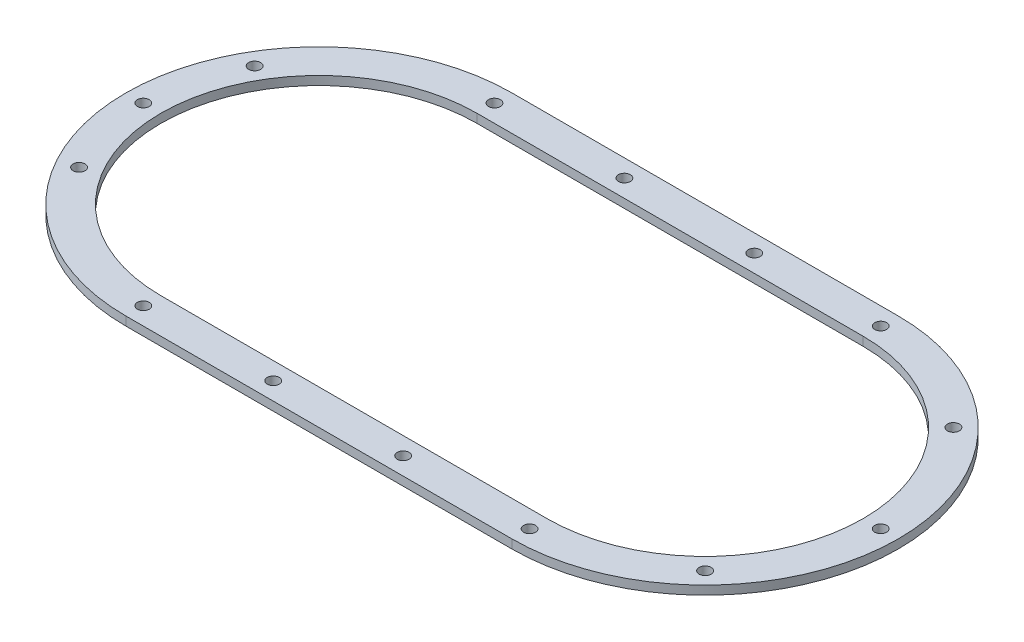
SolidWorks part; units mm, degrees
ref_plane "Front Plane" through (0, 0, 0) normal (0, 0, 1) x (1, 0, 0)
ref_plane "Top Plane" through (0, 0, 0) normal (0, 1, 0) x (1, 0, 0)
ref_plane "Right Plane" through (0, 0, 0) normal (1, 0, 0) x (0, 0, -1)
sketch "Sketch1" plane through (0, 0, 0) normal (0, 1, 0) x (1, 0, 0)
  line L0 (0, 0) -> (220, 0) construction
  line L1 (0, 110) -> (220, 110)
  line L2 (0, -110) -> (220, -110)
  line L3 (0, 90) -> (220, 90)
  line L4 (0, -90) -> (220, -90)
  line L5 (0, 100) -> (220, 100) construction
  line L6 (0, -100) -> (220, -100) construction
  line L7 (-110, 0) -> (330, 0) construction
  line L8 (0, 0) -> (-95.2628, 55) construction
  line L9 (220, 0) -> (297.7817, 77.7817) construction
  arc A0 (0, 110) -> (0, -110) centre (0, 0) ccw
  arc A1 (220, -110) -> (220, 110) centre (220, 0) ccw
  arc A2 (220, -90) -> (220, 90) centre (220, 0) ccw
  arc A3 (0, 90) -> (0, -90) centre (0, 0) ccw
  arc A4 (220, -100) -> (220, 100) centre (220, 0) ccw construction
  arc A5 (0, 100) -> (0, -100) centre (0, 0) ccw construction
  point P3 (110, 0)
  dimension "D2" = 110
  dimension "D1" = 220
  dimension "D5" = 30
  dimension "D6" = 45
  dimension "D3" = 20
  dimension "D4" = 10
extrude "Boss-Extrude1" add sketch "Sketch1" along normal blind 5
hole_wizard "Tap Drill for M8x1.25 Tap1" positions "Sketch2" profile "Sketch3" hole size "M8x1.25" standard "ANSI Metric" end condition through all
sketch "Sketch2" plane through (0, 5, 0) normal (0, 1, 0) x (1, 0, 0)
  line L6 (0, -100) -> (220, -100)
  line L7 (220, 100) -> (0, 100)
  line L8 (0, -100) -> (220, -100) construction
  line L9 (220, 100) -> (0, 100) construction
  line L10 (-100, 0) -> (330, 0) construction
  line L13 (0, 0) -> (-95.2628, 55) construction
  line L18 (220, 0) -> (297.7817, 77.7817) construction
  arc A6 (0, 100) -> (0, -100) centre (0, 0) ccw
  arc A7 (220, -100) -> (220, 100) centre (220, 0) ccw
  arc A8 (0, 100) -> (0, -100) centre (0, 0) ccw construction
  arc A9 (220, -100) -> (220, 100) centre (220, 0) ccw construction
  arc A10 (220, -110) -> (220, 110) centre (220, 0) ccw construction
  arc A11 (0, 110) -> (0, -110) centre (0, 0) ccw construction
  point P33 (0, -100)
  point P36 (220, 100)
  point P37 (-100, 0)
  point P68 (-86.6025, 50)
  point P72 (0, 100)
  point P74 (74, 100)
  point P76 (148, 100)
  point P78 (290.7107, 70.7107)
  point P80 (320, 0)
  point P83 (290.7107, -70.7107)
  point P84 (220, -100)
  point P85 (148, -100)
  point P86 (74, -100)
  point P87 (-86.6025, -50)
  dimension "D2" = 30
  dimension "D3" = 45
  dimension "D4" = 220
  dimension "D5" = 74
  dimension "D6" = 74
  dimension "D1" = 10
sketch "Sketch3" plane through (-86.6025, 5, 50) normal (1, 0, 0) x (0, 0, 1)
  line L0 (0, 0) -> (0, 5)
  line L1 (0, 5) -> (3.4, 5)
  line L2 (3.4, 5) -> (3.4, 0)
  line L5 (3.4, 0) -> (0, 0)
  line L11 (0, -6.35) -> (0, 107.95) construction
  dimension "Thru Hole Dia." = 6.8
  dimension "Thru Hole Depth" = 5
